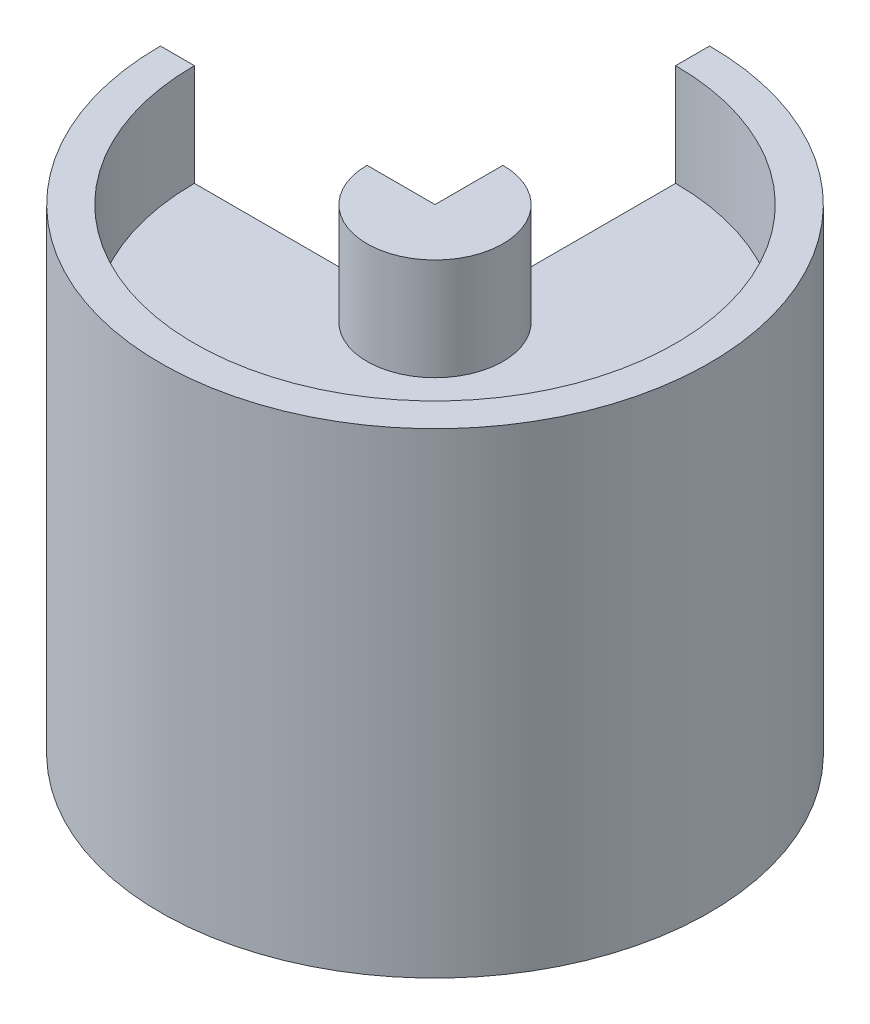
SolidWorks part; units mm, degrees
ref_plane "Front Plane" through (0, 0, 0) normal (0, 0, 1) x (1, 0, 0)
ref_plane "Top Plane" through (0, 0, 0) normal (0, 1, 0) x (1, 0, 0)
ref_plane "Right Plane" through (0, 0, 0) normal (1, 0, 0) x (0, 0, -1)
sketch "Sketch1" plane through (0, 0, 0) normal (1, 0, 0) x (0, 0, -1)
  line L3 (22.479, 35.4984) -> (22.479, 45.0234)
  line L4 (22.479, 45.0234) -> (25.654, 45.0234)
  line L5 (25.654, 45.0234) -> (25.654, 0.5734)
  line L6 (25.654, 0.5734) -> (22.479, 0.5734)
  line L7 (22.479, 0.5734) -> (22.479, 32.3234)
  line L8 (22.479, 32.3234) -> (6.35, 32.3234)
  line L12 (0, 45.0234) -> (0, 0) construction
  line L13 (22.479, 35.4984) -> (6.35, 35.4984)
  line L14 (6.35, 35.4984) -> (6.35, 45.0234)
  line L15 (6.35, 45.0234) -> (3.175, 45.0234)
  line L16 (3.175, 45.0234) -> (3.175, 0.5734)
  line L17 (3.175, 0.5734) -> (6.35, 0.5734)
  line L19 (6.35, 32.3234) -> (6.35, 0.5734)
  dimension "D1" = 44.45
  dimension "D2" = 16.129
  dimension "D3" = 3.175
  dimension "D4" = 31.75
  dimension "D5" = 16.129
  dimension "D6" = 9.525
  dimension "D7" = 3.175
revolve "Revolve2" add sketch "Sketch1" angle 270 about L12
sketch "Sketch2" plane through (0, 45.0234, 0) normal (0, 1, 0) x (1, 0, 0)
  line L0 (0, 6.35) -> (0, 3.175)
  line L1 (-6.35, 0) -> (-3.175, 0)
  line L3 (-3.175, 0) -> (0, 0)
  line L4 (0, 0) -> (0, 3.175)
  arc A1 (0, 6.35) -> (-6.35, 0) centre (0, 0) cw
extrude "Boss-Extrude1" add sketch "Sketch2" against normal through all
